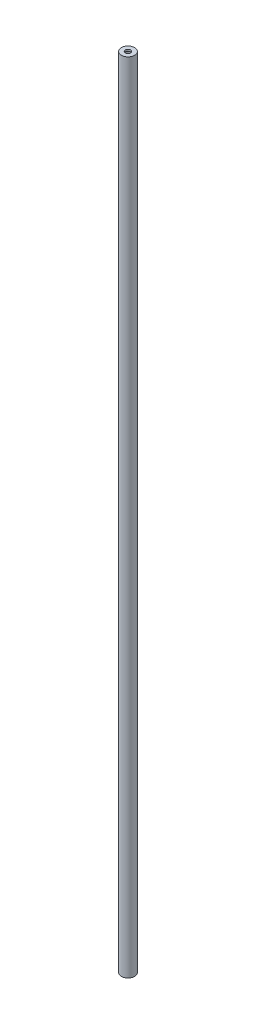
SolidWorks part; units mm, degrees
material "Gray Cast Iron"
ref_plane "Front Plane" through (0, 0, 0) normal (0, 0, 1) x (1, 0, 0)
ref_plane "Top Plane" through (0, 0, 0) normal (0, 1, 0) x (1, 0, 0)
ref_plane "Right Plane" through (0, 0, 0) normal (1, 0, 0) x (0, 0, -1)
sketch "Sketch3" plane through (0, 0, 0) normal (0, 1, 0) x (1, 0, 0)
  circle A0 centre (0, 0) radius 7.5
  dimension "D1" = 15
extrude "Boss-Extrude1" add sketch "Sketch3" along normal blind 900
shell "Shell2" thickness 2
sketch "Sketch4" plane through (0, 900, 0) normal (0, 1, 0) x (1, 0, 0)
  circle A0 centre (0, 0) radius 3
  dimension "6" = 6
extrude "Cut-Extrude1" cut sketch "Sketch4" against normal through all both and the other way through all
